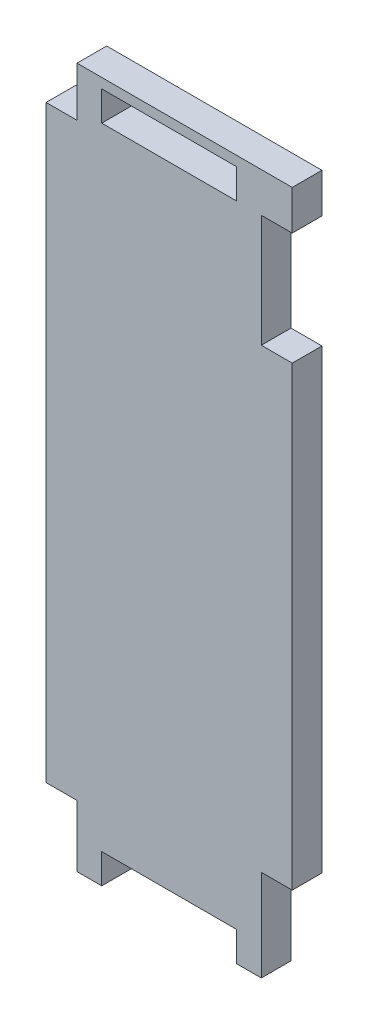
SolidWorks part; units mm, degrees
ref_plane "Front Plane" through (0, 0, 0) normal (0, 0, 1) x (1, 0, 0)
ref_plane "Top Plane" through (0, 0, 0) normal (0, 1, 0) x (1, 0, 0)
ref_plane "Right Plane" through (0, 0, 0) normal (1, 0, 0) x (0, 0, -1)
sketch "Sketch1" plane through (0, 0, 0) normal (0, 0, 1) x (1, 0, 0)
  line L0 (0, 6.731) -> (-3.175, 6.731)
  line L1 (-3.175, 6.731) -> (-3.175, -3.048)
  line L2 (-5.715, 64.77) -> (-19.558, 64.77) construction
  line L3 (-5.715, 64.77) -> (-19.558, 64.77)
  line L4 (-3.175, -3.048) -> (-5.715, -3.048)
  line L5 (-5.715, -3.048) -> (-5.715, 0)
  line L6 (-5.715, 0) -> (-19.558, 0)
  line L7 (-19.558, 0) -> (-19.558, -3.048)
  line L8 (-19.558, 64.77) -> (-19.558, 67.818) construction
  line L9 (-5.715, 67.818) -> (-19.558, 67.818) construction
  line L10 (-5.715, 64.77) -> (-5.715, 67.818) construction
  line L11 (-19.558, 64.77) -> (-19.558, 67.818)
  line L12 (-22.098, 63.754) -> (-25.273, 63.754)
  line L13 (-22.098, 63.754) -> (-25.273, 63.754)
  line L14 (-25.273, 63.754) -> (-25.273, 3.2766)
  line L15 (-25.273, 63.754) -> (-25.273, 3.2766)
  line L16 (-19.558, -3.048) -> (-22.098, -3.048)
  line L17 (-22.098, -3.048) -> (-22.098, 3.2766)
  line L18 (-22.098, 3.2766) -> (-25.273, 3.2766)
  line L19 (-25.273, 3.2766) -> (-25.273, 63.754)
  line L20 (-25.273, 63.754) -> (-22.098, 63.754)
  line L21 (-22.098, 63.754) -> (-22.098, 68.834)
  line L22 (-22.098, 68.834) -> (0, 68.834)
  line L23 (0, 68.834) -> (0, 64.77)
  line L24 (0, 64.77) -> (-3.175, 64.77)
  line L25 (-3.175, 64.77) -> (-3.175, 53.213)
  line L26 (-3.175, 53.213) -> (0, 53.213)
  line L27 (0, 53.213) -> (0, 6.35)
  line L28 (-25.273, 3.2766) -> (-22.098, 3.2766)
  line L29 (-25.273, 3.2766) -> (-22.098, 3.2766)
  line L30 (-22.098, 3.2766) -> (-22.098, -3.048)
  line L31 (-22.098, 3.2766) -> (-22.098, -3.048)
  line L32 (-5.715, 67.818) -> (-19.558, 67.818)
  line L33 (-5.715, 64.77) -> (-5.715, 67.818)
  line L46 (-22.098, -3.048) -> (-19.558, -3.048)
  line L47 (-22.098, -3.048) -> (-19.558, -3.048)
  line L48 (-19.558, -3.048) -> (-19.558, 0)
  line L49 (-19.558, -3.048) -> (-19.558, 0)
  line L50 (-19.558, 0) -> (-5.715, 0)
  line L51 (-19.558, 0) -> (-5.715, 0)
  line L52 (-5.715, 0) -> (-5.715, -3.048)
  line L53 (-5.715, 0) -> (-5.715, -3.048)
  line L54 (-5.715, -3.048) -> (-3.175, -3.048)
  line L55 (-5.715, -3.048) -> (-3.175, -3.048)
  line L56 (-3.175, -3.048) -> (-3.175, 6.35)
  line L57 (-3.175, -3.048) -> (-3.175, 6.35)
  line L58 (-3.175, 6.35) -> (0, 6.35)
  line L59 (-3.175, 6.35) -> (0, 6.35)
  line L60 (0, 6.35) -> (0, 53.213)
  line L61 (0, 6.35) -> (0, 53.213)
  line L62 (0, 53.213) -> (-3.175, 53.213)
  line L63 (0, 53.213) -> (-3.175, 53.213)
  line L64 (-3.175, 53.213) -> (-3.175, 64.77)
  line L65 (-3.175, 53.213) -> (-3.175, 64.77)
  line L66 (-3.175, 64.77) -> (0, 64.77)
  line L67 (-3.175, 64.77) -> (0, 64.77)
  line L68 (0, 64.77) -> (0, 68.834)
  line L69 (0, 64.77) -> (0, 68.834)
  line L70 (0, 68.834) -> (-22.098, 68.834)
  line L71 (0, 68.834) -> (-22.098, 68.834)
  line L72 (-22.098, 68.834) -> (-22.098, 63.754)
  line L73 (-22.098, 68.834) -> (-22.098, 63.754)
  dimension "D1" = 0
extrude "Boss-Extrude1" add sketch "Sketch1" along normal blind 3.048 contours L27 L26 L25 L24 L23 L22 L21 L13 L15 L18 L17 L16 L7 L6 L5 L4 L1 L0 L33 L3 L11 L32 | L1 L59 L27 L0
